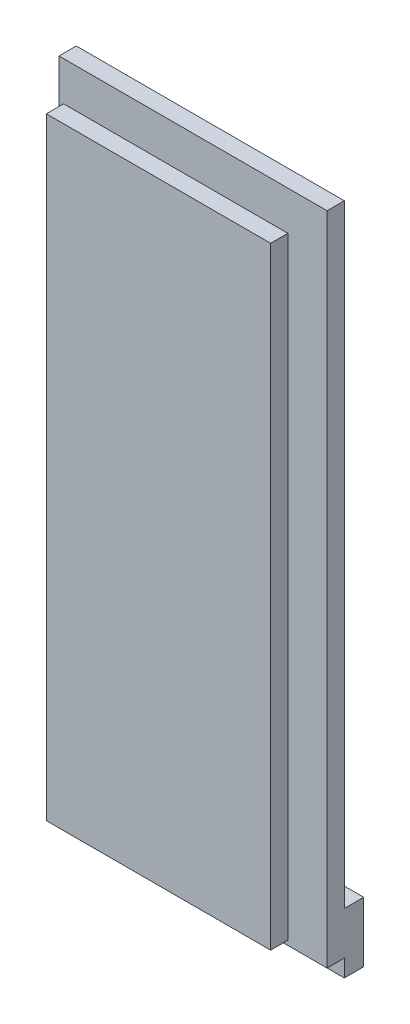
SolidWorks part; units mm, degrees
ref_plane "Front Plane" through (0, 0, 0) normal (0, 0, 1) x (1, 0, 0)
ref_plane "Top Plane" through (0, 0, 0) normal (0, 1, 0) x (1, 0, 0)
ref_plane "Right Plane" through (0, 0, 0) normal (1, 0, 0) x (0, 0, -1)
sketch "Sketch2" plane through (0, 0, 0) normal (0, 0, 1) x (1, 0, 0)
  line L0 (0, 62.023) -> (0, -81.7673) construction
  line L1 (-57.3015, 0) -> (61.1645, 0) construction
  line L3 (-15.5702, 38.1) -> (15.5702, 38.1)
  line L4 (-15.5702, 38.1) -> (-15.5702, -38.1)
  line L5 (-15.5702, -38.1) -> (15.5702, -38.1)
  line L6 (15.5702, 38.1) -> (15.5702, -38.1)
  dimension "D1" = 31.1404
  dimension "D2" = 76.2
extrude "Extrude1" add sketch "Sketch2" along normal blind 2.0066
sketch "Sketch3" plane through (0, 0, 2.0066) normal (0, 0, 1) x (1, 0, 0)
  line L0 (0, 41.1551) -> (0, -41.1551) construction
  line L1 (-19.1047, 0) -> (19.9463, 0) construction
  line L3 (-11.0236, 33.5534) -> (11.0236, 33.5534)
  line L4 (-11.0236, 33.5534) -> (-11.0236, -33.5534)
  line L5 (-11.0236, -33.5534) -> (11.0236, -33.5534)
  line L6 (11.0236, 33.5534) -> (11.0236, -33.5534)
  dimension "D1" = 22.0472
  dimension "D2" = 67.1068
extrude "Extrude2" add sketch "Sketch3" along normal blind 2.0066
sketch "Sketch4" plane through (0, 0, 4.0132) normal (0, 0, 1) x (1, 0, 0)
  line L0 (0, 40.9867) -> (0, -41.3234) construction
  line L1 (-19.6097, 0) -> (19.4414, 0) construction
  line L3 (-13.0302, 35.56) -> (13.0302, 35.56)
  line L4 (-13.0302, 35.56) -> (-13.0302, -35.56)
  line L5 (-13.0302, -35.56) -> (13.0302, -35.56)
  line L6 (13.0302, 35.56) -> (13.0302, -35.56)
  dimension "D1" = 71.12
  dimension "D2" = 26.0604
extrude "Extrude3" add sketch "Sketch4" along normal blind 2.0066
sketch "Sketch5" plane through (0, 0, 0) normal (0, 0, -1) x (-1, 0, 0)
  line L0 (-15.5702, -38.1) -> (-15.5702, 38.1) construction
  line L1 (-15.5702, -33.1) -> (15.5702, -33.1)
  line L2 (-15.5702, -33.1) -> (-15.5702, -40.1)
  line L3 (-15.5702, -40.1) -> (15.5702, -40.1)
  line L4 (15.5702, -33.1) -> (15.5702, -40.1)
  line L5 (15.5702, -38.1) -> (-15.5702, -38.1) construction
  line L6 (15.5702, 38.1) -> (15.5702, -38.1) construction
  dimension "D1" = 5
  dimension "D2" = 2
extrude "Extrude4" add sketch "Sketch5" along normal blind 2.25
